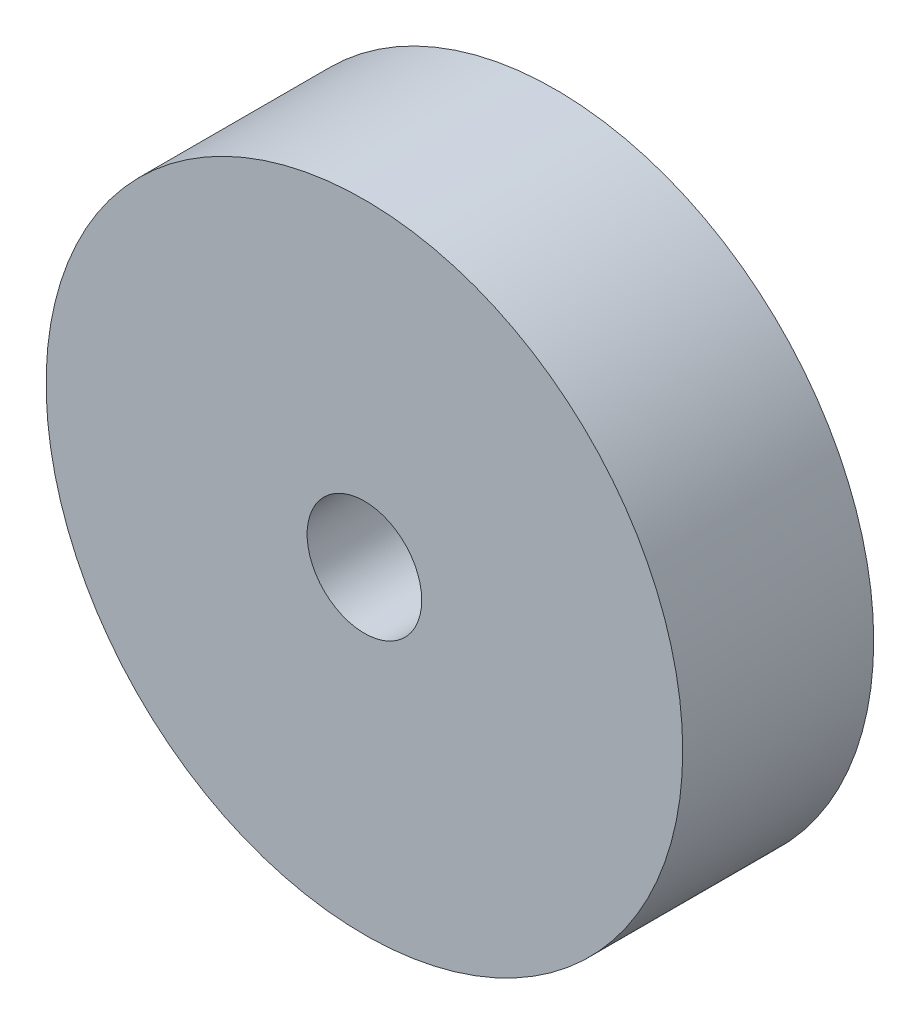
SolidWorks part; units mm, degrees
ref_plane "Alzado" through (0, 0, 0) normal (0, 0, 1) x (1, 0, 0)
ref_plane "Planta" through (0, 0, 0) normal (0, 1, 0) x (1, 0, 0)
ref_plane "Vista lateral" through (0, 0, 0) normal (1, 0, 0) x (0, 0, -1)
sketch "Croquis1" plane through (0, 0, 0) normal (0, 0, 1) x (1, 0, 0)
  circle A0 centre (0, 0) radius 5
  circle A1 centre (0, 0) radius 0.9
  dimension "D1" = 10
  dimension "D2" = 1.8
extrude "Saliente-Extruir1" add sketch "Croquis1" along normal blind 3
